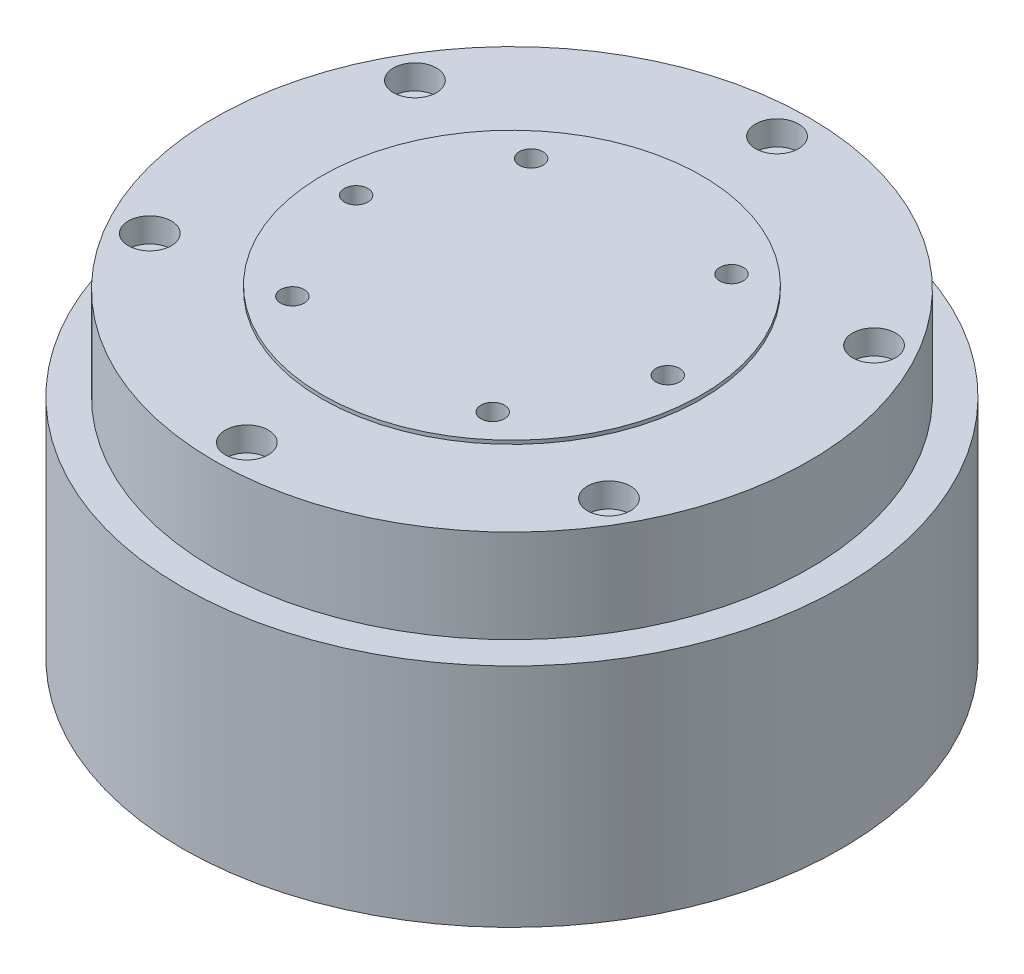
SolidWorks part; units mm, degrees
ref_plane "前视基准面" through (0, 0, 0) normal (0, 0, 1) x (1, 0, 0)
ref_plane "上视基准面" through (0, 0, 0) normal (0, 1, 0) x (1, 0, 0)
ref_plane "右视基准面" through (0, 0, 0) normal (1, 0, 0) x (0, 0, -1)
sketch "草图1" plane through (0, 0, 0) normal (0, 1, 0) x (1, 0, 0)
  circle A0 centre (0, 0) radius 46
  dimension "D1" = 92
extrude "凸台-拉伸1" add sketch "草图1" along normal blind 31.6
sketch "草图2" plane through (0, 31.6, 0) normal (0, 1, 0) x (1, 0, 0)
  circle A0 centre (0, 0) radius 41.5
  dimension "D1" = 83
extrude "凸台-拉伸2" add sketch "草图2" along normal blind 13
sketch "草图3" plane through (0, 31.6, 0) normal (0, 1, 0) x (1, 0, 0)
  circle A0 centre (0, 0) radius 26.5
  dimension "D1" = 53
extrude "凸台-拉伸3" add sketch "草图3" along normal blind 13.5
sketch "草图4" plane through (0, 45.1, 0) normal (0, 1, 0) x (1, 0, 0)
  line L0 (0, 0) -> (13.9806, 16.6615) construction
  line L1 (0, -24.805) -> (0, 24.805) construction
  line L2 (0, 0) -> (-13.9806, 16.6615) construction
  line L3 (-24.805, 0) -> (24.805, 0) construction
  circle A0 centre (0, 0) radius 21.75 construction
  circle A1 centre (-21.75, 0) radius 1.5
  circle A2 centre (21.75, 0) radius 1.5
  circle A3 centre (13.9806, 16.6615) radius 1.5
  circle A4 centre (-13.9806, 16.6615) radius 1.5
  circle A5 centre (13.9806, -16.6615) radius 1.5
  circle A6 centre (-13.9806, -16.6615) radius 1.5
  dimension "D1" = 43.5
  dimension "D3" = 3
  dimension "D2" = 80
extrude "切除-拉伸1" cut sketch "草图4" against normal blind 10
hole_wizard "M4 螺纹孔1" positions "3D草图1" profile "草图6" tap size "M4" standard "GB"
sketch3d "3D草图1"
  circle A0 centre (13.9806, 35.1, 16.6615) radius 1.5 construction
  circle A1 centre (21.75, 45.1, 0) radius 1.5 construction
  circle A2 centre (13.9806, 45.1, -16.6615) radius 1.5 construction
  circle A3 centre (-13.9806, 45.1, -16.6615) radius 1.5 construction
  circle A4 centre (-21.75, 45.1, 0) radius 1.5 construction
  circle A5 centre (-13.9806, 45.1, 16.6615) radius 1.5 construction
  point P0 (-13.9806, 45.1, 16.6615)
  point P2 (-21.75, 45.1, 0)
  point P4 (-13.9806, 45.1, -16.6615)
  point P6 (13.9806, 45.1, -16.6615)
  point P8 (21.75, 45.1, 0)
  point P10 (13.9806, 45.1, 16.6615)
  point P15 (13.9806, 36.6, 16.6615)
  point P19 (21.75, 46.6, 0)
  point P23 (13.9806, 46.6, -16.6615)
  point P26 (-13.9806, 46.6, -16.6615)
  point P29 (-21.75, 46.6, 0)
  point P32 (-13.9806, 46.6, 16.6615)
sketch "草图6" plane through (-13.9806, 45.1, 16.6615) normal (1, 0, 0) x (0, 0, 1)
  line L0 (0, 0) -> (0, 11.0914)
  line L1 (0, 11.0914) -> (1.65, 10.1)
  line L2 (1.65, 10.1) -> (1.65, 0)
  line L5 (1.65, 0) -> (0, 0)
  line L10 (0, 11.0914) -> (-1.65, 10.1) construction
  line L11 (0, -6.35) -> (0, 107.95) construction
  dimension "螺纹孔钻头直径" = 3.3
  dimension "螺纹孔钻头深度" = 10.1
  dimension "导头角度" = 118
cosmetic thread "孔螺蚊线1" parameters "D1"=8, "D2"=4
cosmetic thread "孔螺蚊线2" parameters "D1"=8, "D2"=4
cosmetic thread "孔螺蚊线3" parameters "D1"=8, "D2"=4
cosmetic thread "孔螺蚊线4" parameters "D1"=8, "D2"=4
cosmetic thread "孔螺蚊线5" parameters "D1"=8, "D2"=4
cosmetic thread "孔螺蚊线6" parameters "D1"=8, "D2"=4
sketch "草图7" plane through (0, 44.6, 0) normal (0, 1, 0) x (1, 0, 0)
  circle A0 centre (0, 0) radius 37 construction
  circle A1 centre (0, 37) radius 1
  circle A2 centre (32.0429, 18.5) radius 1
  circle A3 centre (32.0429, -18.5) radius 1
  circle A4 centre (0, -37) radius 1
  circle A5 centre (-32.0429, -18.5) radius 1
  circle A6 centre (-32.0429, 18.5) radius 1
  point P6 (-35.9009, 8.9511)
  point P7 (4.0755, 36.7749)
  point P17 (0, 0)
  point P18 (0, 0)
  dimension "D1" = 74
  dimension "D2" = 2
  dimension "D3" = 6
hole_wizard "M3 六角圆柱头螺钉的柱形沉头孔1" positions "3D草图2" profile "草图8" counterbore size "M3" standard "GB"
sketch3d "3D草图2"
  point P0 (32.0429, 44.6, -18.5)
  point P3 (32.0429, 44.6, 18.5)
  point P6 (0, 44.6, 37)
  point P9 (-32.0429, 44.6, 18.5)
  point P12 (-32.0429, 44.6, -18.5)
  point P15 (0, 44.6, -37)
sketch "草图8" plane through (32.0429, 44.6, -18.5) normal (1, 0, 0) x (0, 0, 1)
  line L0 (0, 0) -> (0, 8.5215)
  line L1 (0, 8.5215) -> (1.7, 7.5)
  line L2 (1.7, 7.5) -> (1.7, 3.4)
  line L3 (1.7, 3.4) -> (3, 3.4)
  line L4 (3, 3.4) -> (3, 0)
  line L5 (3, 0) -> (0, 0)
  line L10 (0, 8.5215) -> (-1.7, 7.5) construction
  line L11 (0, -6.35) -> (0, 107.95) construction
  dimension "孔直径" = 3.4
  dimension "孔深度" = 7.5
  dimension "柱形沉头孔直径" = 6
  dimension "柱形沉头孔深度" = 3.4
  dimension "导头角度" = 118
sketch "草图9" plane through (0, 0, 0) normal (0, -1, 0) x (1, 0, 0)
  line L1 (-13.2772, -19) -> (16.7228, -19)
  line L2 (-13.2772, -19) -> (-13.2772, -34)
  line L3 (-13.2772, -34) -> (16.7228, -34)
  line L4 (16.7228, -19) -> (16.7228, -34)
  circle A0 centre (0, 0) radius 46 construction
  dimension "D1" = 30
  dimension "D2" = 15
  dimension "D3" = 12
extrude "凸台-拉伸4" add sketch "草图9" along normal blind 4
